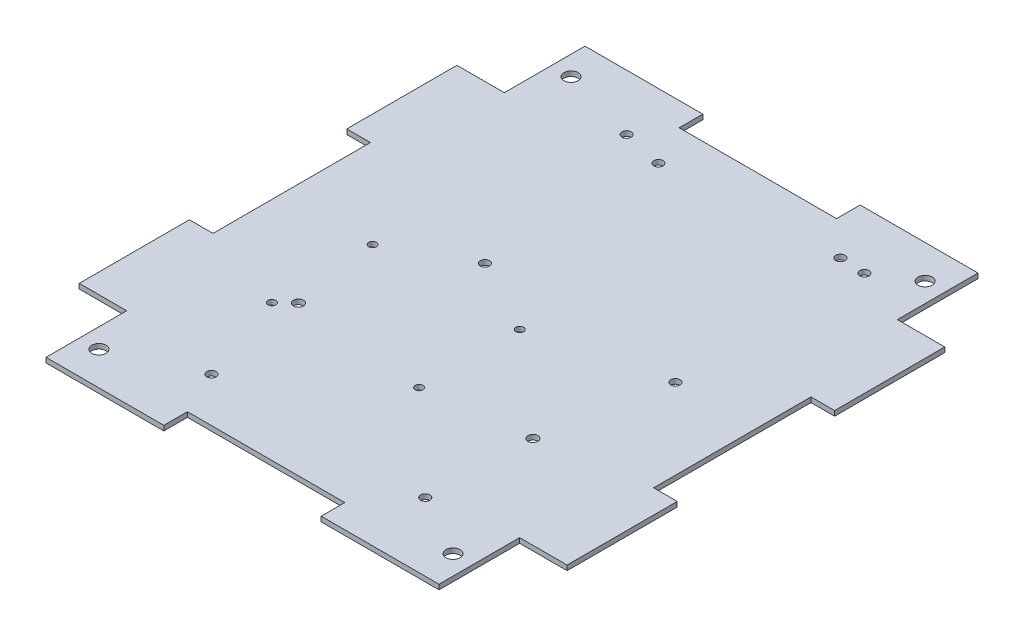
SolidWorks part; units mm, degrees
ref_plane "Front Plane" through (0, 0, 0) normal (0, 0, 1) x (1, 0, 0)
ref_plane "Top Plane" through (0, 0, 0) normal (0, 1, 0) x (1, 0, 0)
ref_plane "Right Plane" through (0, 0, 0) normal (1, 0, 0) x (0, 0, -1)
sketch "Sketch1" plane through (0, 0, 0) normal (0, 1, 0) x (1, 0, 0)
  line L0 (-25.4, 86.995) -> (-63.4314, 86.995)
  line L1 (-88.9, -101.6) -> (88.9, -101.6) construction
  line L2 (101.6, -88.9) -> (101.6, 88.9) construction
  line L3 (88.9, 101.6) -> (-88.9, 101.6) construction
  line L4 (-78.74, -60.96) -> (-63.4314, -60.96)
  line L5 (-63.4314, -60.96) -> (-63.4314, -86.995)
  line L6 (-63.4314, -86.995) -> (-25.4, -86.995)
  line L7 (63.4314, -86.995) -> (63.4314, -60.96)
  line L8 (63.4314, -60.96) -> (78.74, -60.96)
  line L9 (78.74, -60.96) -> (78.74, -25.4)
  line L10 (78.74, 60.96) -> (63.4314, 60.96)
  line L11 (63.4314, 60.96) -> (63.4314, 86.995)
  line L12 (63.4314, 86.995) -> (25.4, 86.995)
  line L13 (-63.4314, 86.995) -> (-63.4314, 60.96)
  line L14 (-63.4314, 60.96) -> (-78.74, 60.96)
  line L15 (-78.74, 60.96) -> (-78.74, 25.4)
  line L16 (-78.74, -25.4) -> (-78.74, -60.96)
  line L17 (-78.74, -25.4) -> (-71.12, -25.4)
  line L19 (-78.74, 25.4) -> (-71.12, 25.4)
  line L20 (-71.12, -25.4) -> (-71.12, 25.4)
  line L22 (-25.4, 86.995) -> (-25.4, 79.375)
  line L23 (-25.4, 79.375) -> (25.4, 79.375)
  line L24 (25.4, 86.995) -> (25.4, 79.375)
  line L25 (78.74, 25.4) -> (71.12, 25.4)
  line L27 (78.74, -25.4) -> (71.12, -25.4)
  line L28 (71.12, 25.4) -> (71.12, -25.4)
  line L30 (25.4, -86.995) -> (25.4, -79.375)
  line L31 (25.4, -79.375) -> (-25.4, -79.375)
  line L32 (-25.4, -86.995) -> (-25.4, -79.375)
  line L33 (78.74, 25.4) -> (78.74, 60.96)
  line L34 (25.4, -86.995) -> (63.4314, -86.995)
  line L35 (-101.6, 88.9) -> (-101.6, -88.9) construction
  arc A0 (88.9, -101.6) -> (101.6, -88.9) centre (88.9, -88.9) ccw construction
  arc A1 (-101.6, -88.9) -> (-88.9, -101.6) centre (-88.9, -88.9) ccw construction
  arc A2 (101.6, 88.9) -> (88.9, 101.6) centre (88.9, 88.9) ccw construction
  arc A3 (-101.6, 88.9) -> (-88.9, 101.6) centre (-88.9, 88.9) cw construction
  circle A4 centre (-57.15, 76.2) radius 2.286
  circle A5 centre (57.15, 76.2) radius 2.286
  circle A6 centre (57.15, -76.2) radius 2.286
  circle A7 centre (-57.15, -76.2) radius 2.286
  point P3 (0, 101.6)
  point P5 (101.6, 0)
  point P13 (101.6, 101.6)
  point P16 (-101.6, 101.6)
  point P38 (-71.12, 0)
  point P55 (0, -79.375)
  point P56 (0, 79.375)
  point P57 (71.12, 0)
  dimension "D2" = 12.7
  dimension "D11" = 4.572
  dimension "D8" = 44.45
  dimension "D1" = 203.2
  dimension "D3" = 203.2
  dimension "D4" = 22.86
  dimension "D5" = 15.3086
  dimension "D6" = 35.56
  dimension "D7" = 173.99
  dimension "D12" = 50.8
  dimension "D13" = 25.4
  dimension "D14" = 44.45
  dimension "D15" = 25.4
  dimension "D18" = 7.62
extrude "Main Body" add sketch "Sketch1" along normal blind 1.5875
sketch "Sketch12" plane through (0, 0, 0) normal (0, -1, 0) x (1, 0, 0)
  line L1 (-45, -80) -> (45, -80)
  line L2 (-45, -80) -> (-45, 80)
  line L3 (-45, 80) -> (45, 80)
  line L4 (45, -80) -> (45, 80)
  line L5 (-45, -80) -> (45, 80) construction
  line L6 (-45, 80) -> (45, -80) construction
  line L7 (-39.779, -55.547) -> (-27.7357, -55.547)
  line L8 (-39.779, -55.547) -> (-39.779, -29.6043)
  line L9 (-39.779, -29.6043) -> (-27.7357, -29.6043)
  line L10 (-27.7357, -55.547) -> (-27.7357, -29.6043)
  line L11 (-39.779, -55.547) -> (-27.7357, -29.6043) construction
  line L12 (-39.779, -29.6043) -> (-27.7357, -55.547) construction
  line L13 (-29.9932, -76.7863) -> (-5.1713, -76.7863)
  line L14 (-29.9932, -76.7863) -> (-29.9932, -67.2902)
  line L15 (-29.9932, -67.2902) -> (-5.1713, -67.2902)
  line L16 (-5.1713, -76.7863) -> (-5.1713, -67.2902)
  line L17 (-29.9932, -76.7863) -> (-5.1713, -67.2902) construction
  line L18 (-29.9932, -67.2902) -> (-5.1713, -76.7863) construction
  line L28 (-78.74, 60.96) -> (-78.74, 25.4)
  line L29 (-78.74, 25.4) -> (-71.12, 25.4)
  line L30 (-71.12, 25.4) -> (-71.12, -25.4)
  line L31 (-71.12, -25.4) -> (-78.74, -25.4)
  line L32 (-78.74, -25.4) -> (-78.74, -60.96)
  line L33 (-78.74, -60.96) -> (-63.4314, -60.96)
  line L34 (-63.4314, -60.96) -> (-63.4314, -86.995)
  line L35 (-63.4314, -86.995) -> (-25.4, -86.995)
  line L36 (-25.4, -86.995) -> (-25.4, -79.375)
  line L37 (-25.4, -79.375) -> (25.4, -79.375)
  line L38 (25.4, -79.375) -> (25.4, -86.995)
  line L39 (25.4, -86.995) -> (63.4314, -86.995)
  line L40 (63.4314, -86.995) -> (63.4314, -60.96)
  line L41 (63.4314, -60.96) -> (78.74, -60.96)
  line L42 (78.74, -60.96) -> (78.74, -25.4)
  line L43 (78.74, -25.4) -> (71.12, -25.4)
  line L44 (71.12, -25.4) -> (71.12, 25.4)
  line L45 (71.12, 25.4) -> (78.74, 25.4)
  line L46 (78.74, 25.4) -> (78.74, 60.96)
  line L47 (78.74, 60.96) -> (63.4314, 60.96)
  line L48 (63.4314, 60.96) -> (63.4314, 86.995)
  line L49 (63.4314, 86.995) -> (25.4, 86.995)
  line L50 (25.4, 86.995) -> (25.4, 79.375)
  line L51 (25.4, 79.375) -> (-25.4, 79.375)
  line L52 (-25.4, 79.375) -> (-25.4, 86.995)
  line L53 (-25.4, 86.995) -> (-63.4314, 86.995)
  line L54 (-63.4314, 86.995) -> (-63.4314, 60.96)
  line L55 (-63.4314, 60.96) -> (-78.74, 60.96)
  line L56 (-78.74, 60.96) -> (-78.74, 25.4)
  line L57 (-78.74, 25.4) -> (-71.12, 25.4)
  line L58 (-71.12, 25.4) -> (-71.12, -25.4)
  line L59 (-71.12, -25.4) -> (-78.74, -25.4)
  line L60 (-78.74, -25.4) -> (-78.74, -60.96)
  line L61 (-78.74, -60.96) -> (-63.4314, -60.96)
  line L62 (-63.4314, -60.96) -> (-63.4314, -86.995)
  line L63 (-63.4314, -86.995) -> (-25.4, -86.995)
  line L64 (-25.4, -86.995) -> (-25.4, -79.375)
  line L65 (-25.4, -79.375) -> (25.4, -79.375)
  line L66 (25.4, -79.375) -> (25.4, -86.995)
  line L67 (25.4, -86.995) -> (63.4314, -86.995)
  line L68 (63.4314, -86.995) -> (63.4314, -60.96)
  line L69 (63.4314, -60.96) -> (78.74, -60.96)
  line L70 (78.74, -60.96) -> (78.74, -25.4)
  line L71 (78.74, -25.4) -> (71.12, -25.4)
  line L72 (71.12, -25.4) -> (71.12, 25.4)
  line L73 (71.12, 25.4) -> (78.74, 25.4)
  line L74 (78.74, 25.4) -> (78.74, 60.96)
  line L75 (78.74, 60.96) -> (63.4314, 60.96)
  line L76 (63.4314, 60.96) -> (63.4314, 86.995)
  line L77 (63.4314, 86.995) -> (25.4, 86.995)
  line L78 (25.4, 86.995) -> (25.4, 79.375)
  line L79 (25.4, 79.375) -> (-25.4, 79.375)
  line L80 (-25.4, 79.375) -> (-25.4, 86.995)
  line L81 (-25.4, 86.995) -> (-63.4314, 86.995)
  line L82 (-63.4314, 86.995) -> (-63.4314, 60.96)
  line L83 (-63.4314, 60.96) -> (-78.74, 60.96)
  circle A0 centre (-32, -69) radius 1.5
  circle A1 centre (37, -69) radius 1.5
  circle A2 centre (37, 65) radius 1.5
  circle A3 centre (-32, 65) radius 1.5
  circle A4 centre (-42.25, 2.75) radius 1.25
  circle A5 centre (-42.25, 35.25) radius 1.25
  circle A6 centre (5.25, 2.75) radius 1.25
  circle A7 centre (5.25, 35.25) radius 1.25
  point P2 (0, 0)
  point P12 (-33.7573, -42.5756)
  point P22 (-17.5822, -72.0382)
  dimension "D4" = 3
  dimension "D9" = 2.5
  dimension "D2" = 90
  dimension "D3" = 160
  dimension "D5" = 11
  dimension "D6" = 145
  dimension "D7" = 8
  dimension "D8" = 77
  dimension "D10" = 32.5
  dimension "D11" = 47.5
  dimension "D12" = 2.75
  dimension "D13" = 44.75
  dimension "D1" = 0
extrude "Cut-Extrude3" cut sketch "Sketch12" against normal up to next contours A3 | A2 | A1 | A0 | A5 | A7 | A6 | A4
sketch "Sketch13" plane through (0, 1.5875, 0) normal (0, 1, 0) x (1, 0, 0)
  line L0 (-53.34, 63.1) -> (-66.34, 63.1)
  line L1 (-53.34, 73.1) -> (52.66, 73.1)
  line L2 (-53.34, 73.1) -> (-53.34, 3.1)
  line L3 (-53.34, 3.1) -> (52.66, 3.1)
  line L4 (52.66, 73.1) -> (52.66, 3.1)
  line L5 (-53.34, 73.1) -> (52.66, 3.1) construction
  line L6 (-53.34, 3.1) -> (52.66, 73.1) construction
  line L7 (-66.34, 63.1) -> (-66.34, 52.6)
  line L8 (-66.34, 52.6) -> (-53.34, 52.6)
  line L9 (-53.34, 23.6) -> (-66.34, 23.6)
  line L10 (-66.34, 23.6) -> (-66.34, 13.1)
  line L11 (-66.34, 13.1) -> (-53.34, 13.1)
  line L13 (-40.5, -74.1) -> (40.5, -74.1)
  line L14 (-40.5, -74.1) -> (-40.5, -2.1)
  line L15 (-40.5, -2.1) -> (40.5, -2.1)
  line L16 (40.5, -74.1) -> (40.5, -2.1)
  line L17 (-40.5, -74.1) -> (40.5, -2.1) construction
  line L18 (-40.5, -2.1) -> (40.5, -74.1) construction
  line L28 (-78.74, -25.4) -> (-78.74, -60.96)
  line L29 (-78.74, -60.96) -> (-63.4314, -60.96)
  line L30 (-63.4314, -60.96) -> (-63.4314, -86.995)
  line L31 (-63.4314, -86.995) -> (-25.4, -86.995)
  line L32 (-25.4, -86.995) -> (-25.4, -79.375)
  line L33 (-25.4, -79.375) -> (25.4, -79.375)
  line L34 (25.4, -79.375) -> (25.4, -86.995)
  line L35 (25.4, -86.995) -> (63.4314, -86.995)
  line L36 (63.4314, -86.995) -> (63.4314, -60.96)
  line L37 (63.4314, -60.96) -> (78.74, -60.96)
  line L38 (78.74, -60.96) -> (78.74, -25.4)
  line L39 (78.74, -25.4) -> (71.12, -25.4)
  line L40 (71.12, -25.4) -> (71.12, 25.4)
  line L41 (71.12, 25.4) -> (78.74, 25.4)
  line L42 (78.74, 25.4) -> (78.74, 60.96)
  line L43 (78.74, 60.96) -> (63.4314, 60.96)
  line L44 (63.4314, 60.96) -> (63.4314, 86.995)
  line L45 (63.4314, 86.995) -> (25.4, 86.995)
  line L46 (25.4, 86.995) -> (25.4, 79.375)
  line L47 (25.4, 79.375) -> (-25.4, 79.375)
  line L48 (-25.4, 79.375) -> (-25.4, 86.995)
  line L49 (-25.4, 86.995) -> (-63.4314, 86.995)
  line L50 (-63.4314, 86.995) -> (-63.4314, 60.96)
  line L51 (-63.4314, 60.96) -> (-78.74, 60.96)
  line L52 (-78.74, 60.96) -> (-78.74, 25.4)
  line L53 (-78.74, 25.4) -> (-71.12, 25.4)
  line L54 (-71.12, 25.4) -> (-71.12, -25.4)
  line L55 (-71.12, -25.4) -> (-78.74, -25.4)
  line L56 (-78.74, -25.4) -> (-78.74, -60.96)
  line L57 (-78.74, -60.96) -> (-63.4314, -60.96)
  line L58 (-63.4314, -60.96) -> (-63.4314, -86.995)
  line L59 (-63.4314, -86.995) -> (-25.4, -86.995)
  line L60 (-25.4, -86.995) -> (-25.4, -79.375)
  line L61 (-25.4, -79.375) -> (25.4, -79.375)
  line L62 (25.4, -79.375) -> (25.4, -86.995)
  line L63 (25.4, -86.995) -> (63.4314, -86.995)
  line L64 (63.4314, -86.995) -> (63.4314, -60.96)
  line L65 (63.4314, -60.96) -> (78.74, -60.96)
  line L66 (78.74, -60.96) -> (78.74, -25.4)
  line L67 (78.74, -25.4) -> (71.12, -25.4)
  line L68 (71.12, -25.4) -> (71.12, 25.4)
  line L69 (71.12, 25.4) -> (78.74, 25.4)
  line L70 (78.74, 25.4) -> (78.74, 60.96)
  line L71 (78.74, 60.96) -> (63.4314, 60.96)
  line L72 (63.4314, 60.96) -> (63.4314, 86.995)
  line L73 (63.4314, 86.995) -> (25.4, 86.995)
  line L74 (25.4, 86.995) -> (25.4, 79.375)
  line L75 (25.4, 79.375) -> (-25.4, 79.375)
  line L76 (-25.4, 79.375) -> (-25.4, 86.995)
  line L77 (-25.4, 86.995) -> (-63.4314, 86.995)
  line L78 (-63.4314, 86.995) -> (-63.4314, 60.96)
  line L79 (-63.4314, 60.96) -> (-78.74, 60.96)
  line L80 (-78.74, 60.96) -> (-78.74, 25.4)
  line L81 (-78.74, 25.4) -> (-71.12, 25.4)
  line L82 (-71.12, 25.4) -> (-71.12, -25.4)
  line L83 (-71.12, -25.4) -> (-78.74, -25.4)
  circle A0 centre (45.16, 7.6) radius 1.5
  circle A1 centre (45.16, 68.6) radius 1.5
  circle A2 centre (-18.84, 66.1) radius 1.5
  circle A3 centre (-18.84, 10.1) radius 1.5
  circle A6 centre (-37.85, -31.1) radius 1.625
  circle A7 centre (37.85, -31.1) radius 1.625
  point P2 (-0.34, 38.1)
  point P42 (0, -38.1)
  point P55 (40.5, -38.1)
  point P60 (0, 0)
  point P66 (0, -74.1)
  dimension "D4" = 3
  dimension "D23" = 2.65
  dimension "D21" = 3.25
  dimension "D2" = 106
  dimension "D3" = 70
  dimension "D5" = 4.5
  dimension "D6" = 7.5
  dimension "D7" = 4.5
  dimension "D8" = 7
  dimension "D9" = 7
  dimension "D10" = 71.5
  dimension "D11" = 38.1
  dimension "D12" = 53.34
  dimension "D13" = 10.5
  dimension "D14" = 13
  dimension "D15" = 10
  dimension "D16" = 10
  dimension "D17" = 72
  dimension "D18" = 81
  dimension "D19" = 38.1
  dimension "D20" = 0
  dimension "D22" = 2.65
  dimension "D24" = 43
  dimension "D1" = 0
extrude "Cut-Extrude4" cut sketch "Sketch13" against normal up to next
